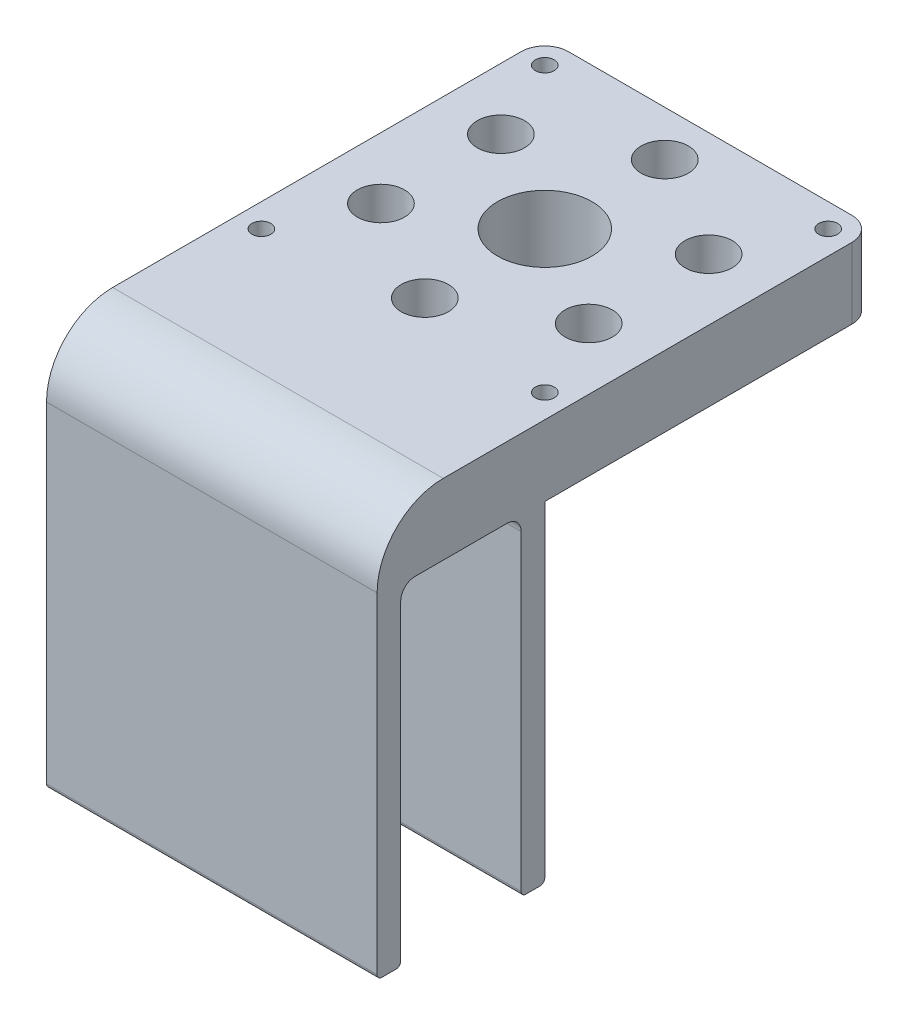
SolidWorks part; units mm, degrees
ref_plane "Front Plane" through (0, 0, 0) normal (0, 0, 1) x (1, 0, 0)
ref_plane "Top Plane" through (0, 0, 0) normal (0, 1, 0) x (1, 0, 0)
ref_plane "Right Plane" through (0, 0, 0) normal (1, 0, 0) x (0, 0, -1)
sketch "Sketch1" plane through (0, 0, 0) normal (0, 1, 0) x (1, 0, 0)
  line L1 (35, 35) -> (-35, 35)
  line L2 (35, 35) -> (35, -35)
  line L3 (35, -35) -> (-35, -35)
  line L4 (-35, 35) -> (-35, -35)
  circle A11 centre (0, 25.4) radius 2.6
  circle A12 centre (21.997, 12.7) radius 2.6
  circle A13 centre (21.997, -12.7) radius 2.6
  circle A14 centre (0, -25.4) radius 2.6
  circle A15 centre (-21.997, -12.7) radius 2.6
  circle A16 centre (-21.997, 12.7) radius 2.6
  circle A17 centre (0, 0) radius 10
  circle A18 centre (-30, 30) radius 2
  circle A19 centre (30, 30) radius 2
  circle A20 centre (30, -30) radius 2
  circle A21 centre (-30, -30) radius 2
  point P13 (0, 0)
  point P27 (0, 0)
  point P31 (-6.943, 27.6647)
  dimension "D1" = 25.4
  dimension "D2" = 5.2
  dimension "D4" = 30
  dimension "D7" = 20
  dimension "D8" = 4
  dimension "D6" = 4
  dimension "D5" = 30
  dimension "D9" = 35
  dimension "D10" = 70
  dimension "D11" = 35
  dimension "D12" = 70
  dimension "D3" = 6
extrude "Boss-Extrude1" add sketch "Sketch1" along normal blind 15
sketch "Sketch2" plane through (0, 15, 0) normal (0, 1, 0) x (1, 0, 0)
  circle A0 centre (-21.997, -12.7) radius 2.6 construction
  circle A1 centre (0, -25.4) radius 2.6 construction
  circle A2 centre (21.997, -12.7) radius 2.6 construction
  circle A3 centre (21.997, 12.7) radius 2.6 construction
  circle A4 centre (0, 25.4) radius 2.6 construction
  circle A5 centre (-21.997, 12.7) radius 2.6 construction
  circle A6 centre (-21.997, -12.7) radius 2.6
  circle A7 centre (0, -25.4) radius 2.6
  circle A8 centre (21.997, -12.7) radius 2.6
  circle A9 centre (21.997, 12.7) radius 2.6
  circle A10 centre (0, 25.4) radius 2.6
  circle A11 centre (-21.997, 12.7) radius 2.6
  circle A18 centre (-21.997, -12.7) radius 5
  circle A19 centre (0, -25.4) radius 5
  circle A20 centre (21.997, -12.7) radius 5
  circle A21 centre (21.997, 12.7) radius 5
  circle A22 centre (0, 25.4) radius 5
  circle A23 centre (-21.997, 12.7) radius 5
  dimension "D1" = 2.4
extrude "Cut-Extrude1" cut sketch "Sketch2" against normal offset from surface (11 mm away) 4 up to face at (-30, 0, 32)
sketch "Sketch3" plane through (-35, 0, 0) normal (-1, 0, 0) x (0, 0, 1)
  line L0 (-35, 15) -> (35, 15) construction
  line L2 (35, 0) -> (35, -70)
  line L3 (35, -70) -> (40, -70)
  line L4 (40, -3) -> (40, -70)
  line L5 (65.5, -70) -> (70.5, -70)
  line L6 (65.5, -70) -> (65.5, -3)
  line L8 (70.5, -70) -> (70.5, 0)
  line L9 (62.5, 0) -> (43, 0)
  line L10 (70.5, 0) -> (70.5, 1)
  line L11 (56.5, 15) -> (35, 15)
  line L12 (35, 0) -> (35, 15)
  arc A0 (70.5, 1) -> (56.5, 15) centre (56.5, 1) ccw
  arc A1 (65.5, -3) -> (62.5, 0) centre (62.5, -3) ccw
  arc A2 (43, 0) -> (40, -3) centre (43, -3) ccw
  point P19 (56.5, 25.1082)
  point P22 (70.5, -5.8436)
  dimension "D6" = 14
  dimension "D7" = 3
  dimension "D1" = 5
  dimension "D2" = 70
  dimension "D3" = 5
  dimension "D4" = 70
  dimension "D5" = 25.5
  dimension "D8" = 70
extrude "Boss-Extrude2" add sketch "Sketch3" against normal blind 70
fillet "Fillet1" radius 5 2 edges at (35, 7.5, -35) (-35, 7.5, -35)
fillet "Fillet2" radius 1 4 edges at (0, -70, 70.5) (0, -70, 65.5) (0, -70, 35) (0, -70, 40)
